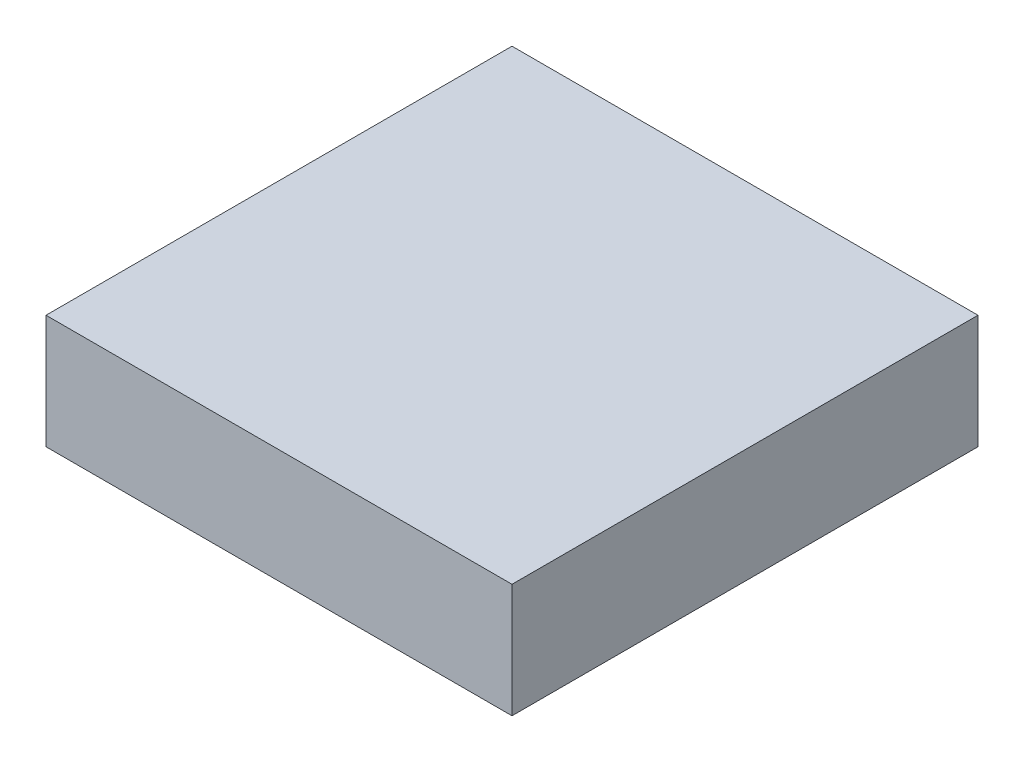
SolidWorks part; units mm, degrees
ref_plane "Front Plane" through (0, 0, 0) normal (0, 0, 1) x (1, 0, 0)
ref_plane "Top Plane" through (0, 0, 0) normal (0, 1, 0) x (1, 0, 0)
ref_plane "Right Plane" through (0, 0, 0) normal (1, 0, 0) x (0, 0, -1)
ref_plane "button bottom" through (0, 99.4015, 0) normal (0, -1, 0) x (-1, 0, 0)
sketch "Sketch2" plane through (0, 99.4015, 0) normal (0, -1, 0) x (-1, 0, 0)
  line L1 (-45.4103, -138.6552) -> (-36.4103, -138.6552)
  line L2 (-45.4103, -138.6552) -> (-45.4103, -147.6552)
  line L3 (-45.4103, -147.6552) -> (-36.4103, -147.6552)
  line L4 (-36.4103, -138.6552) -> (-36.4103, -147.6552)
  line L5 (-45.4103, -138.6552) -> (-36.4103, -147.6552) construction
  line L6 (-45.4103, -147.6552) -> (-36.4103, -138.6552) construction
  point P0 (-40.9103, -143.1552)
  dimension "D1" = 9
  dimension "D2" = 9
extrude "Boss-Extrude1" add sketch "Sketch2" against normal blind 2.2
